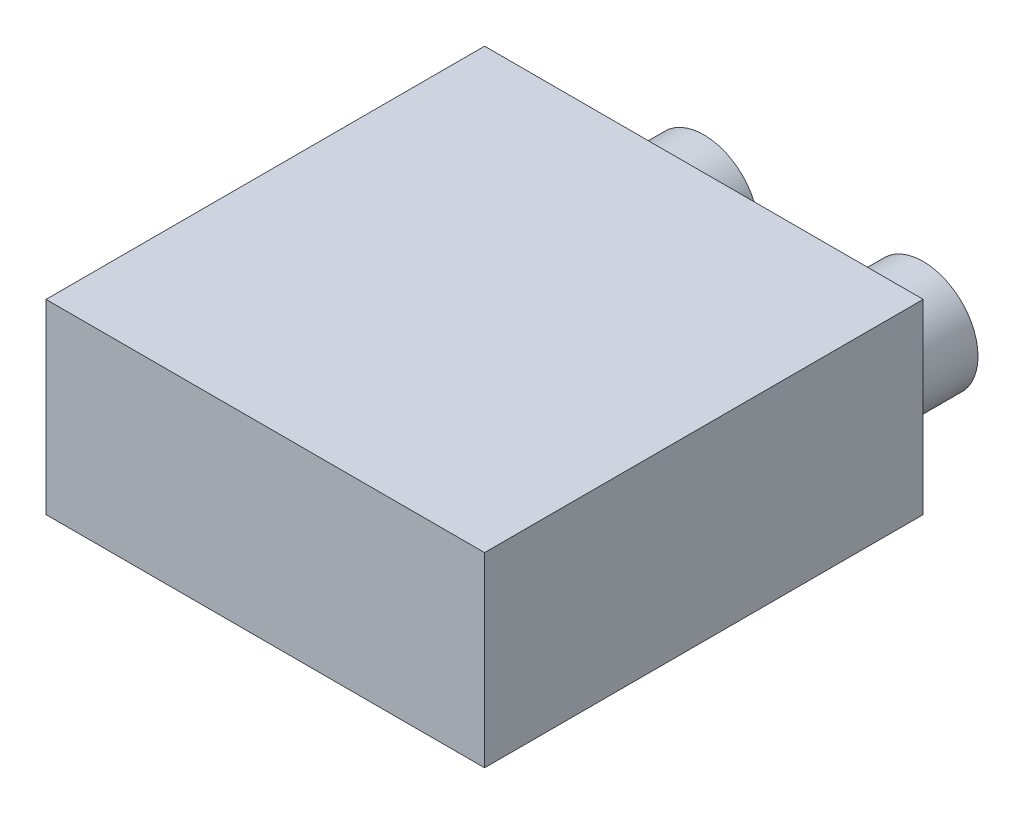
SolidWorks part; units mm, degrees
ref_plane "Front Plane" through (0, 0, 0) normal (0, 0, 1) x (1, 0, 0)
ref_plane "Top Plane" through (0, 0, 0) normal (0, 1, 0) x (1, 0, 0)
ref_plane "Right Plane" through (0, 0, 0) normal (1, 0, 0) x (0, 0, -1)
sketch "Sketch1" plane through (0, 0, 0) normal (0, 1, 0) x (1, 0, 0)
  line L1 (-20, 20) -> (20, 20)
  line L2 (-20, 20) -> (-20, -20)
  line L3 (-20, -20) -> (20, -20)
  line L4 (20, 20) -> (20, -20)
  line L5 (-20, 20) -> (20, -20) construction
  line L6 (-20, -20) -> (20, 20) construction
  point P0 (0, 0)
  dimension "D1" = 40
  dimension "D2" = 40
extrude "Boss-Extrude1" add sketch "Sketch1" along normal blind 17
sketch "Sketch2" plane through (0, 0, -20) normal (0, 0, -1) x (-1, 0, 0)
  line L0 (-20, 0) -> (20, 0) construction
  line L1 (0, 9.35) -> (0, -9.35) construction
  circle A0 centre (10, 5) radius 5
  dimension "D2" = 10
  dimension "D1" = 5
  dimension "D3" = 10
extrude "Boss-Extrude2" add sketch "Sketch2" along normal blind 10
mirror "Mirror1" about plane through (0, 0, 0) normal (1, 0, 0) of "Boss-Extrude2"
